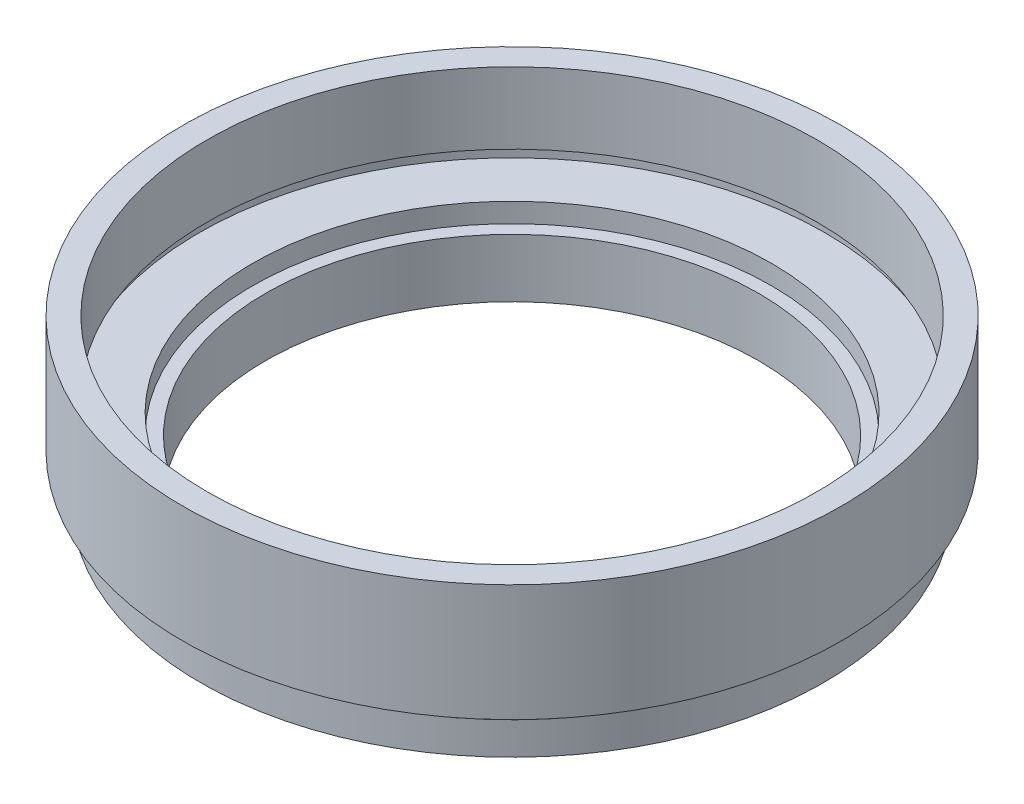
SolidWorks part; units mm, degrees
ref_plane "前视基准面" through (0, 0, 0) normal (0, 0, 1) x (1, 0, 0)
ref_plane "上视基准面" through (0, 0, 0) normal (0, 1, 0) x (1, 0, 0)
ref_plane "右视基准面" through (0, 0, 0) normal (1, 0, 0) x (0, 0, -1)
sketch "草图1" plane through (0, 0, 0) normal (0, 0, 1) x (1, 0, 0)
  line L0 (0, 0) -> (0, 21.8535) construction
  line L1 (19, 0) -> (24, 0)
  line L2 (24, 0) -> (24, 2.5)
  line L3 (24, 2.5) -> (23.5, 2.5)
  line L4 (23.5, 2.5) -> (23.5, 3.5)
  line L5 (23.5, 3.5) -> (25.4, 3.5)
  line L6 (25.4, 3.5) -> (25.4, 12.5)
  line L7 (25.4, 12.5) -> (23.5, 12.5)
  line L8 (23.5, 12.5) -> (23.5, 7)
  line L9 (23.5, 7) -> (24.1, 7)
  line L10 (24.1, 7) -> (24.1, 6)
  line L11 (24.1, 6) -> (20, 6)
  line L12 (20, 6) -> (20, 4.5)
  line L13 (20, 4.5) -> (19, 4.5)
  line L14 (19, 0) -> (19, 4.5)
  dimension "D1" = 12.5
  dimension "D2" = 25.4
  dimension "D3" = 23.5
  dimension "D4" = 20
  dimension "D5" = 1
  dimension "D6" = 1.5
  dimension "D7" = 19
  dimension "D8" = 24
  dimension "D9" = 1
  dimension "D10" = 3.5
  dimension "D11" = 4.5
  dimension "D12" = 24.1
  dimension "D13" = 23.5
revolve "旋转1" add sketch "草图1" angle 360 about L0
cosmetic thread "装饰螺纹线11"
cosmetic thread "装饰螺纹线12"
